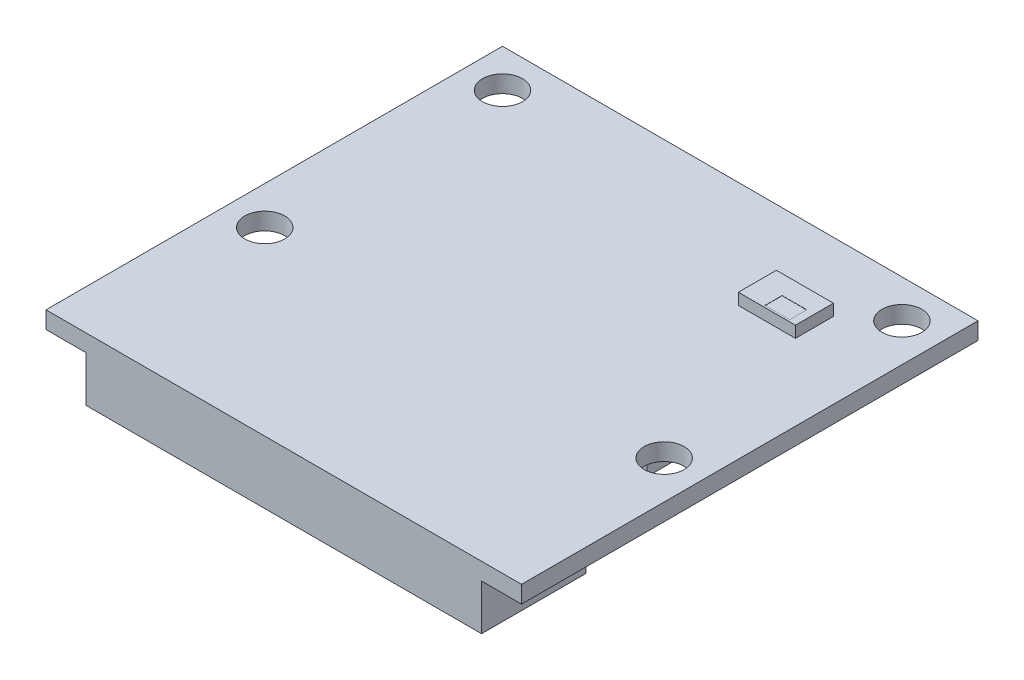
SolidWorks part; units mm, degrees
material "Epoxid, Ungefüllt"
ref_plane "Vorne" through (0, 0, 0) normal (0, 0, 1) x (1, 0, 0)
ref_plane "Oben" through (0, 0, 0) normal (0, 1, 0) x (1, 0, 0)
ref_plane "Rechts" through (0, 0, 0) normal (1, 0, 0) x (0, 0, -1)
sketch "Skizze1" plane through (0, 0, 0) normal (0, 1, 0) x (1, 0, 0)
  line L0 (0, 14.5) -> (0, -9.5) construction
  line L1 (-12.5, 14.5) -> (12.5, 14.5)
  line L2 (-12.5, 14.5) -> (-12.5, -9.5)
  line L3 (-12.5, -9.5) -> (12.5, -9.5)
  line L4 (12.5, 14.5) -> (12.5, -9.5)
  dimension "D1" = 24
  dimension "D2" = 25
  dimension "D3" = 9.5
extrude "PCB" add sketch "Skizze1" against normal blind 0.9
sketch "Skizze2" plane through (0, 0, 0) normal (0, 1, 0) x (1, 0, 0)
  line L0 (12.5, 14.5) -> (-12.5, 14.5) construction
  line L1 (12.5, -9.5) -> (12.5, 14.5) construction
  line L2 (0, 0) -> (0, 9.3158) construction
  circle A0 centre (10.5, 12.5) radius 1.05
  circle A1 centre (10.5, 0) radius 1.05
  circle A2 centre (-10.5, 0) radius 1.05
  circle A3 centre (-10.5, 12.5) radius 1.05
  dimension "D1" = 2.1
  dimension "D2" = 2
  dimension "D3" = 2
  dimension "D4" = 12.5
extrude "Mounting_Holes" cut sketch "Skizze2" against normal through all
sketch "Skizze3" plane through (0, -0.9, 0) normal (0, -1, 0) x (1, 0, 0)
  line L0 (0, 4) -> (0, 0) construction
  line L1 (-10.4, 9.5) -> (10.4, 9.5)
  line L2 (-10.4, 9.5) -> (-10.4, 4)
  line L3 (-10.4, 4) -> (10.4, 4)
  line L4 (10.4, 9.5) -> (10.4, 4)
  line L5 (-12.5, 9.5) -> (12.5, 9.5) construction
  dimension "D1" = 20.8
  dimension "D2" = 5.5
extrude "Connector_closed" add sketch "Skizze3" along normal blind 2.4
sketch "Skizze4" plane through (0, -0.9, 0) normal (0, -1, 0) x (1, 0, 0)
  line L0 (-12.5, -14.5) -> (-12.5, 9.5) construction
  line L1 (-9, -0.9) -> (8.7, -0.9)
  line L2 (-9, -0.9) -> (-9, -12.5)
  line L3 (-9, -12.5) -> (8.7, -12.5)
  line L4 (8.7, -0.9) -> (8.7, -12.5)
  line L5 (12.5, -14.5) -> (-12.5, -14.5) construction
  dimension "D1" = 17.7
  dimension "D2" = 3.5
  dimension "D3" = 2
  dimension "D4" = 13.6
extrude "Components_worst-case_Boundary-Box" add sketch "Skizze4" along normal blind 1.3
sketch "Skizze5" plane through (0, 0, 0) normal (1, 0, 0) x (0, 0, -1)
  line L0 (-9.5, -3.3) -> (-9.5, -0.9) construction
  line L1 (-9.5, 0) -> (14.5, 0) construction
  line L2 (-19.1541, -2.1) -> (0.1541, -2.1) construction
  line L3 (-158.9972, -1.9259) -> (-164.8596, -3.2031)
  spline S0 degree 3 poles (-9.5, -2.1) (-26.0076, -2.1) (-26.235, -0.1149) (-64.4158, -1.6263) (-124.9063, 9.5892) (-158.9972, -1.9259) knots 0 0 0 0 0.321879 0.421879 1 1 1 1
  dimension "D1" = 2.1
  dimension "D2" = 6
sketch "Skizze6" plane through (0, 0, 9.5) normal (0, 0, 1) x (1, 0, 0)
  line L1 (-8, -2.1) -> (8, -2.1)
  line L2 (-8, -2.1) -> (-8, -2.5)
  line L3 (-8, -2.5) -> (8, -2.5)
  line L4 (8, -2.1) -> (8, -2.5)
  dimension "D1" = 16
  dimension "D2" = 0.4
sweep "Cable_156mm_free_Length" [suppressed] add profiles "Skizze6" path "Skizze5"
sketch "Skizze7" plane through (0, 0, 0) normal (0, 1, 0) x (1, 0, 0)
  line L0 (12.5, 14.5) -> (-12.5, 14.5) construction
  line L1 (5.5, 10.9) -> (8.5, 10.9)
  line L2 (5.5, 10.9) -> (5.5, 8.9)
  line L3 (5.5, 8.9) -> (8.5, 8.9)
  line L4 (8.5, 10.9) -> (8.5, 8.9)
  line L5 (12.5, -9.5) -> (12.5, 14.5) construction
  dimension "D1" = 5.6
  dimension "D2" = 3.6
  dimension "D3" = 4
  dimension "D4" = 7
extrude "Components_worst-case_Boundary-Box2" add sketch "Skizze7" along normal blind 0.6
sketch "Skizze8" plane through (0, 0.6, 0) normal (0, 1, 0) x (1, 0, 0)
  line L0 (12.5, -9.5) -> (12.5, 14.5) construction
  line L1 (8.1, 9) -> (6.8, 9)
  line L2 (8.1, 9) -> (8.1, 9.9)
  line L3 (8.1, 9.9) -> (6.8, 9.9)
  line L4 (6.8, 9) -> (6.8, 9.9)
  line L5 (12.5, 14.5) -> (-12.5, 14.5) construction
  dimension "D1" = 1.3
  dimension "D2" = 0.9
  dimension "D3" = 4.4
  dimension "D4" = 4.6
extrude "Status_LED" cut sketch "Skizze8" against normal blind 0.01
